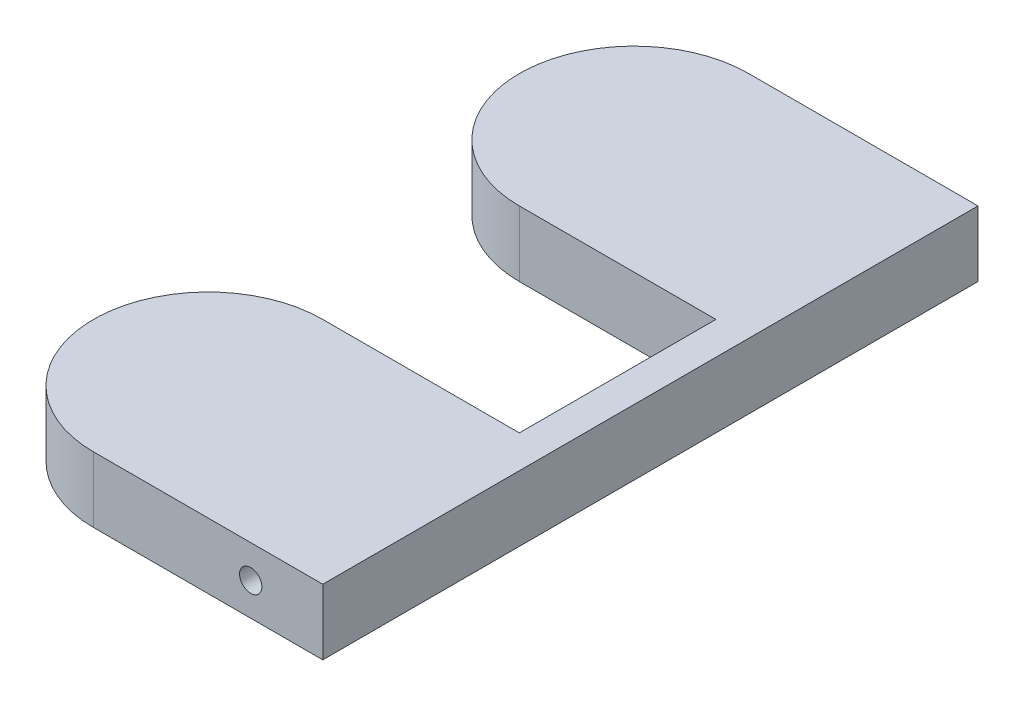
SolidWorks part; units mm, degrees
ref_plane "Front Plane" through (0, 0, 0) normal (0, 0, 1) x (1, 0, 0)
ref_plane "Top Plane" through (0, 0, 0) normal (0, 1, 0) x (1, 0, 0)
ref_plane "Right Plane" through (0, 0, 0) normal (1, 0, 0) x (0, 0, -1)
sketch "Sketch1" plane through (0, 0, 0) normal (0, 1, 0) x (1, 0, 0)
  line L0 (44.9015, 0) -> (-52.9759, 0) construction
  line L1 (5, 50) -> (5, -50)
  line L2 (5, -50) -> (-30, -50)
  line L3 (-30, -15) -> (0, -15)
  line L4 (0, -15) -> (0, 15)
  line L5 (-30, 15) -> (0, 15)
  line L6 (5, 50) -> (-30, 50)
  arc A0 (-30, -50) -> (-30, -15) centre (-30, -32.5) cw
  arc A1 (-30, 50) -> (-30, 15) centre (-30, 32.5) ccw
  point P14 (0, 0)
  point P15 (5, 0)
  dimension "D1" = 5
  dimension "D2" = 30
  dimension "D3" = 15
  dimension "D4" = 35
extrude "Boss-Extrude1" add sketch "Sketch1" along normal blind 10
sketch "Sketch2" plane through (0, 0, 50) normal (0, 0, 1) x (1, 0, 0)
  line L0 (-30, 10) -> (5, 10) construction
  line L1 (5, 10) -> (5, 0) construction
  circle A0 centre (-6, 5) radius 1.705
  dimension "D1" = 3.41
  dimension "D2" = 5
  dimension "D3" = 11
extrude "Cut-Extrude1" cut sketch "Sketch2" against normal blind 15
sketch "Sketch3" plane through (0, 0, 35) normal (0, 0, 1) x (1, 0, 0)
  line L0 (-30, 0) -> (5, 0) construction
  line L1 (-9.65, 0) -> (-2.35, 0)
  line L2 (-9.65, 0) -> (-9.65, 8.65)
  line L3 (-9.65, 8.65) -> (-2.35, 8.65)
  line L4 (-2.35, 0) -> (-2.35, 8.65)
  circle A0 centre (-6, 5) radius 1.705 construction
  dimension "D2" = 3.65
  dimension "D1" = 3.65
  dimension "D3" = 3.65
extrude "Cut-Extrude2" cut sketch "Sketch3" along normal blind 8
sketch "Sketch4" plane through (0, 0, -50) normal (0, 0, -1) x (-1, 0, 0)
  line L0 (-5, 10) -> (30, 10) construction
  line L6 (-5, 10) -> (-5, 0) construction
  circle A0 centre (6, 5) radius 1.705
  dimension "D1" = 3.41
  dimension "D2" = 5
  dimension "D3" = 11
extrude "Cut-Extrude3" cut sketch "Sketch4" against normal blind 15
sketch "Sketch5" plane through (0, 0, -35) normal (0, 0, -1) x (-1, 0, 0)
  line L0 (-5, 0) -> (30, 0) construction
  line L1 (9.65, 8.65) -> (2.35, 8.65)
  line L2 (9.65, 8.65) -> (9.65, 0)
  line L3 (9.65, 0) -> (2.35, 0)
  line L4 (2.35, 8.65) -> (2.35, 0)
  circle A0 centre (6, 5) radius 1.705 construction
  circle A1 centre (6, 5) radius 1.705 construction
  dimension "D1" = 3.65
  dimension "D2" = 3.65
  dimension "D3" = 3.65
extrude "Cut-Extrude4" cut sketch "Sketch5" along normal blind 8
